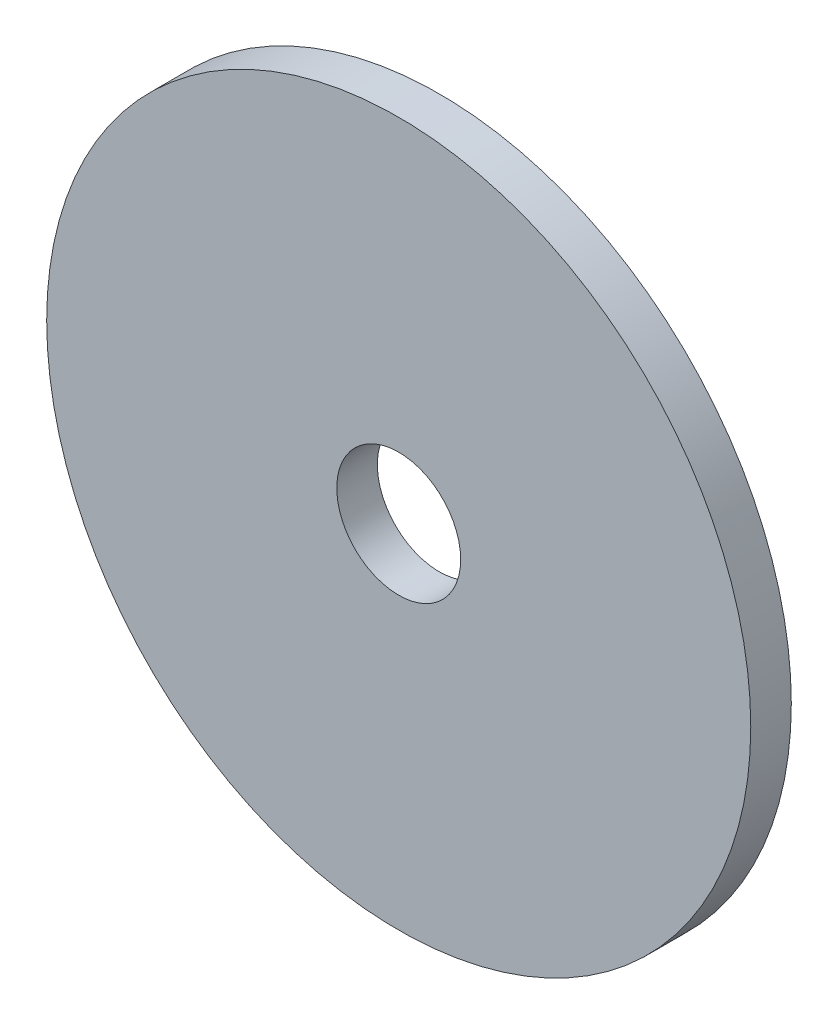
SolidWorks part; units mm, degrees
material "Alloy Steel"
ref_plane "Front Plane" through (0, 0, 0) normal (0, 0, 1) x (1, 0, 0)
ref_plane "Top Plane" through (0, 0, 0) normal (0, 1, 0) x (1, 0, 0)
ref_plane "Right Plane" through (0, 0, 0) normal (1, 0, 0) x (0, 0, -1)
sketch "Sketch1" plane through (0, 0, 0) normal (0, 0, 1) x (1, 0, 0)
  circle A0 centre (0, 0) radius 2.2
  circle A1 centre (0, 0) radius 12.5
  dimension "D1" = 25
  dimension "D2" = 4.4
extrude "Boss-Extrude1" add sketch "Sketch1" along normal blind 1.44
